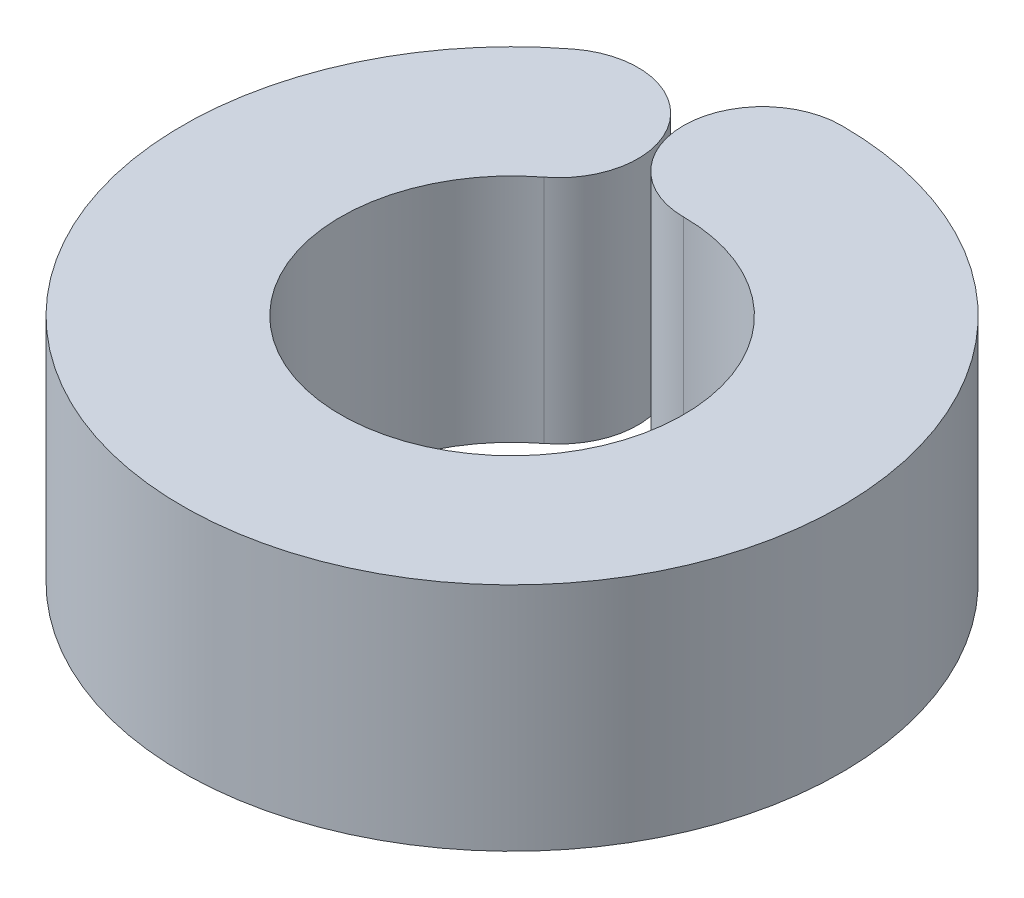
SolidWorks part; units mm, degrees
ref_plane "Front Plane" through (0, 0, 0) normal (0, 0, 1) x (1, 0, 0)
ref_plane "Top Plane" through (0, 0, 0) normal (0, 1, 0) x (1, 0, 0)
ref_plane "Right Plane" through (0, 0, 0) normal (1, 0, 0) x (0, 0, -1)
sketch "Sketch1" plane through (0, 0, 0) normal (0, 1, 0) x (1, 0, 0)
  arc A0 (0, 3.8) -> (-2.3089, 3.0181) centre (0, 0) cw
  arc A1 (0, 2.6) -> (-1.5798, 2.065) centre (0, 0) cw
  arc A2 (0, 5) -> (-3.038, 3.9712) centre (0, 0) cw
  arc A3 (0, 2.6) -> (0, 5) centre (0, 3.8) cw
  arc A4 (-1.5798, 2.065) -> (-3.038, 3.9712) centre (-2.3089, 3.0181) ccw
  point P10 (0, 0)
  point P11 (-2.5415, 3.5918)
  point P12 (-3.397, 2.7965)
  point P13 (-2.4809, 2.8784)
  point P14 (-2.3834, 2.9597)
  point P15 (0, 0)
  point P16 (-2.3089, 3.0181)
  dimension "D1" = 3.8
  dimension "D2" = 1.2
  dimension "D3" = 1.2
extrude "Boss-Extrude1" add sketch "Sketch1" along normal blind 3.5
